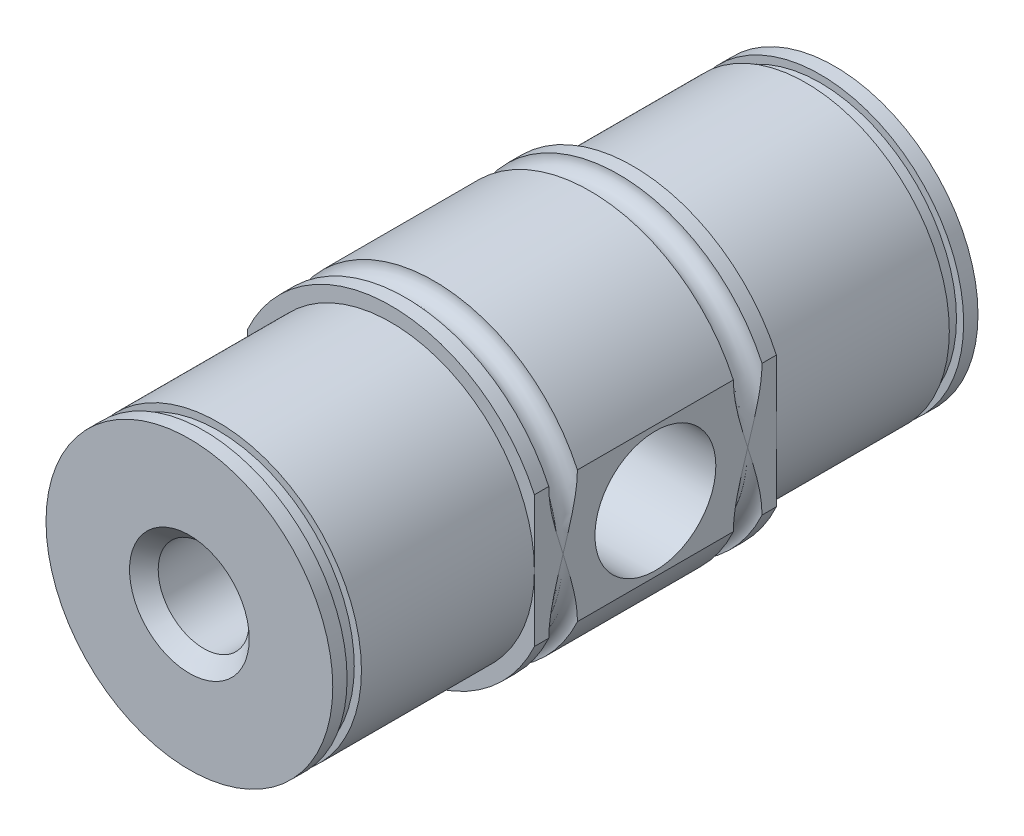
SolidWorks part; units mm, degrees
ref_plane "Front Plane" through (0, 0, 0) normal (0, 0, 1) x (1, 0, 0)
ref_plane "Top Plane" through (0, 0, 0) normal (0, 1, 0) x (1, 0, 0)
ref_plane "Right Plane" through (0, 0, 0) normal (1, 0, 0) x (0, 0, -1)
sketch "Sketch1" plane through (0, 0, 0) normal (0, 0, 1) x (1, 0, 0)
  circle A0 centre (0, 0) radius 11
  dimension "D1" = 22
extrude "Boss-Extrude1" add sketch "Sketch1" along normal blind 16.875
sketch "Sketch2" plane through (0, 0, 0) normal (0, 0, -1) x (-1, 0, 0)
  circle A0 centre (0, 0) radius 10
  dimension "D1" = 20
extrude "Boss-Extrude2" add sketch "Sketch2" along normal blind 14.0625
sketch "Sketch3" plane through (0, 0, 16.875) normal (0, 0, 1) x (1, 0, 0)
  circle A0 centre (0, 0) radius 10
  dimension "D1" = 20
extrude "Boss-Extrude3" add sketch "Sketch3" along normal blind 14.0625
sketch "Sketch5" plane through (0, 0, 0) normal (0, 0, -1) x (-1, 0, 0)
  line L0 (-10, 4.5826) -> (-10, -4.5826)
  line L1 (10, 4.5826) -> (10, -4.5826)
  circle A0 centre (0, 0) radius 11 construction
  circle A1 centre (0, 0) radius 11
  circle A2 centre (0, 0) radius 10 construction
  circle A3 centre (0, 0) radius 10 construction
  circle M4 centre (0, 0) radius 11
extrude "Cut-Extrude4" cut sketch "Sketch5" against normal through all both and the other way through all contours L0 M4 | L1 M4
sketch "Sketch6" plane through (0, 0, 0) normal (1, 0, 0) x (0, 0, -1)
  line L0 (14.0625, 10) -> (13.0625, 10)
  line L1 (14.0625, 10) -> (0, 10) construction
  line L2 (13.0625, 10) -> (13.0625, 9.5)
  line L3 (13.0625, 9.5) -> (12.0625, 9.5)
  line L4 (12.0625, 9.5) -> (12.0625, 10)
  line L5 (12.0625, 10) -> (13.0625, 10)
  line L6 (-8.4375, 11) -> (-8.4375, -11) construction
  line L7 (0, 11) -> (-16.875, 11) construction
  line L8 (-16.875, -11) -> (0, -11) construction
  line L9 (-15.875, 11) -> (-13.875, 11)
  line L10 (-28.9375, 10) -> (-29.9375, 10)
  line L11 (-28.9375, 9.5) -> (-28.9375, 10)
  line L12 (-29.9375, 9.5) -> (-28.9375, 9.5)
  line L13 (-29.9375, 10) -> (-29.9375, 9.5)
  line L14 (-30.9375, 0) -> (14.0625, 0) construction
  line L15 (-30.9375, 10) -> (-30.9375, -10) construction
  line L16 (14.0625, -10) -> (14.0625, 10) construction
  line L17 (-3, 11) -> (-1, 11)
  arc A0 (-15.875, 11) -> (-13.875, 11) centre (-14.875, 11) ccw
  arc A1 (-1, 11) -> (-3, 11) centre (-2, 11) cw
  dimension "D5" = 2
  dimension "D1" = 1
  dimension "D2" = 1
  dimension "D3" = 0.5
revolve "Cut-Revolve1" cut sketch "Sketch6" angle 360 about L14
sketch "Sketch8" plane through (10, 0, 0) normal (1, 0, 0) x (0, 0, -1)
  line L0 (-8.4375, 11) -> (-8.4375, -11) construction
  point P0 (-8.4375, 0)
hole_wizard "3/8-24 Tapped Hole1" positions "Sketch8" profile "Sketch9" tap size "3/8-24" standard "ANSI Inch" end condition through all
sketch "Sketch9" plane through (10, 0, 8.4375) normal (0, 1, 0) x (0, 0, -1)
  line L0 (0, 0) -> (0, 20)
  line L1 (0, 20) -> (4.2164, 20)
  line L2 (4.2164, 20) -> (4.2164, 0)
  line L5 (4.2164, 0) -> (0, 0)
  line L11 (0, -6.35) -> (0, 107.95) construction
  dimension "Thru Tap Drill Dia." = 8.4328
  dimension "Thru Tap Drill Depth" = 20
cosmetic thread "Hole Thread1" parameters "D2"=9.525
sketch "Sketch10" plane through (0, 0, -14.0625) normal (0, 0, -1) x (-1, 0, 0)
  circle A0 centre (0, 0) radius 3.175
  dimension "D1" = 6.35
extrude "Cut-Extrude5" cut sketch "Sketch10" against normal through all and the other way through all
chamfer "Chamfer1" distance 1 angle 45 2 edges at (-3.175, 0, 30.9375) (-3.175, 0, -14.0625)
equation "\"shaft\"= 20"
equation "\"brace\"= 22"
equation "\"shaft length\"= 45"
equation "\"D1@Sketch1\"=\"brace\""
equation "\"D1@Boss-Extrude1\"=\"shaft length\"*(3/8)"
equation "\"D1@Sketch2\"=\"shaft\""
equation "\"D1@Boss-Extrude2\"=\"shaft length\"*(5/16)"
equation "\"D1@Sketch3\"=\"shaft\""
equation "\"D1@Boss-Extrude3\"=\"shaft length\"*(5/16)"
